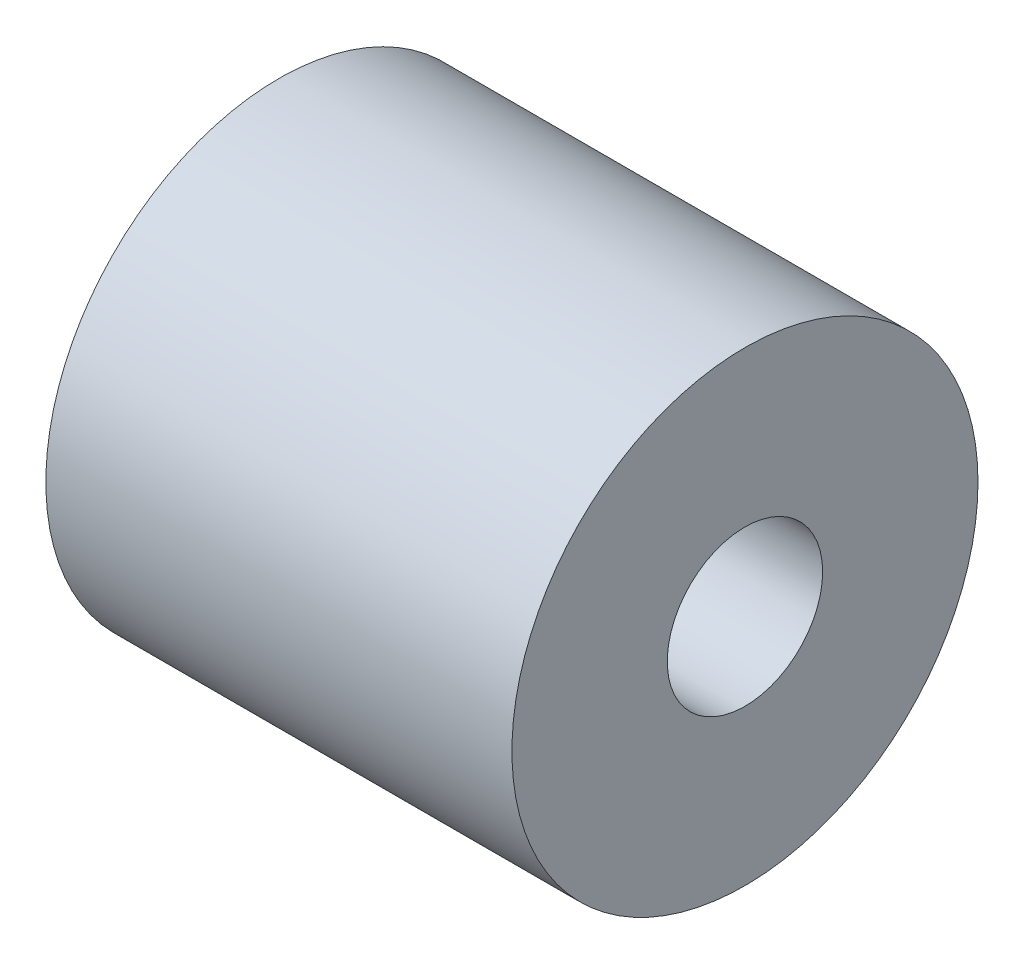
SolidWorks part; units mm, degrees
ref_plane "Спереди" through (0, 0, 0) normal (0, 0, 1) x (1, 0, 0)
ref_plane "Сверху" through (0, 0, 0) normal (0, 1, 0) x (1, 0, 0)
ref_plane "Справа" through (0, 0, 0) normal (1, 0, 0) x (0, 0, -1)
sketch "Эскиз1" plane through (0, 0, 0) normal (0, 0, 1) x (1, 0, 0)
  line L0 (0, 3.175) -> (0, 5)
  line L1 (0, 5) -> (15, 5)
  line L2 (15, 5) -> (15, 15)
  line L3 (15, 15) -> (-15, 15)
  line L4 (-15, 15) -> (-15, 3.175)
  line L5 (-15, 3.175) -> (0, 3.175)
  line L6 (-15, 0) -> (15, 0) construction
  point P9 (0, 0)
  point P10 (-15, 7.9328)
  point P11 (0, 0)
  dimension "D1" = 30
  dimension "D2" = 6.35
  dimension "D3" = 10
  dimension "D4" = 15
  dimension "D5" = 30
revolve "Повернуть1" add sketch "Эскиз1" angle 360 about L6
